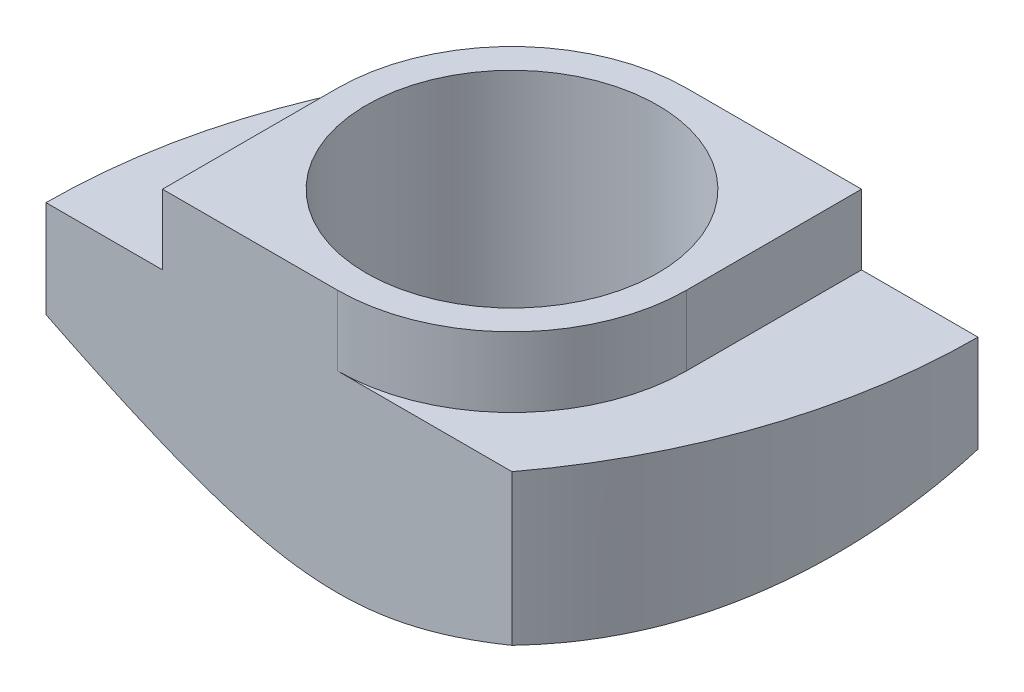
SolidWorks part; units mm, degrees
ref_plane "前视基准面" through (0, 0, 0) normal (0, 0, 1) x (1, 0, 0)
ref_plane "上视基准面" through (0, 0, 0) normal (0, 1, 0) x (1, 0, 0)
ref_plane "右视基准面" through (0, 0, 0) normal (1, 0, 0) x (0, 0, -1)
sketch "草图1" plane through (0, 0, 0) normal (0, 1, 0) x (1, 0, 0)
  line L0 (0, 0) -> (10, 0)
  line L1 (10, 0) -> (10, 6)
  line L2 (10, 6) -> (0, 6)
  line L3 (0, 6) -> (0, 0)
  circle A0 centre (5, 3) radius 2.5
  dimension "D3" = 5
  dimension "D1" = 10
  dimension "D2" = 6
  dimension "D4" = 5
  dimension "D5" = 3
extrude "凸台-拉伸1" add sketch "草图1" along normal blind 3.3
sketch "草图2" plane through (0, 3.3, 0) normal (0, 1, 0) x (1, 0, 0)
  line L0 (0, 6) -> (0, 0) construction
  line L1 (0, 0) -> (10, 0) construction
  line L2 (2, 3) -> (2, 0)
  line L3 (8, 3) -> (8, 6)
  line L4 (10, 6) -> (0, 6) construction
  line L5 (8, 6) -> (5, 6)
  line L6 (2, 0) -> (5, 0)
  circle A0 centre (5, 3) radius 2.5
  arc A1 (5, 0) -> (8, 3) centre (5, 3) ccw
  arc A2 (5, 6) -> (2, 3) centre (5, 3) ccw
  dimension "D3" = 5
  dimension "D4" = 6
  dimension "D1" = 5
  dimension "D2" = 3
extrude "凸台-拉伸2" add sketch "草图2" along normal blind 1.2
ref_plane "基准面1" through (0, 0, -3) normal (0, 0, -1) x (-1, 0, 0)
sketch "草图3" plane through (0, 0, 0) normal (0, 1, 0) x (1, 0, 0)
  line L0 (5, 6) -> (0, 6) construction
  line L5 (5, 6) -> (0, 6)
  line L6 (0, 6) -> (0, 0)
  line L7 (0, 0) -> (2, 0)
  line L8 (2, 6) -> (0, 6)
  line L9 (0, 6) -> (0, 0)
  line L11 (5, 0) -> (10, 0)
  line L12 (10, 0) -> (10, 6)
  line L13 (10, 6) -> (8, 6)
  line L15 (10, 0) -> (10, 6)
  line L16 (5, 0) -> (10, 0) construction
  line L17 (8, 0) -> (10, 0)
  line L20 (2, 0) -> (2, 3)
  line L22 (8, 6) -> (8, 3)
  arc A0 (0, 0) -> (2, 6) centre (10, 0) cw
  arc A3 (5, 6) -> (2, 3) centre (5, 3) ccw
  arc A5 (5, 0) -> (8, 3) centre (5, 3) ccw
  arc A7 (8, 0) -> (10, 6) centre (0, 6) ccw
  dimension "D1" = 0
  dimension "D2" = 0
extrude "切除-拉伸1" cut sketch "草图3" along normal through all
sketch "草图4" plane through (-3, 0, -3) normal (0, 0, 1) x (1, 0, 0)
  line L0 (0, 2.8868) -> (5, 0)
  line L2 (11, 0) -> (13, 0) construction
  line L3 (0, 2.8868) -> (0, 0)
  line L4 (0, 0) -> (5, 0)
  line L10 (8, 4.5) -> (8, 3.3) construction
  line L11 (16, 2.8868) -> (16, 0)
  line L12 (16, 2.8868) -> (11, 0)
  line L13 (16, 0) -> (11, 0)
  dimension "D1" = 2
  dimension "D3" = 30
  dimension "D6" = 5
revolve "切除-旋转1" cut sketch "草图4" angle 360 about axis through (5, 3.3, -3) along (0, -1, 0)
